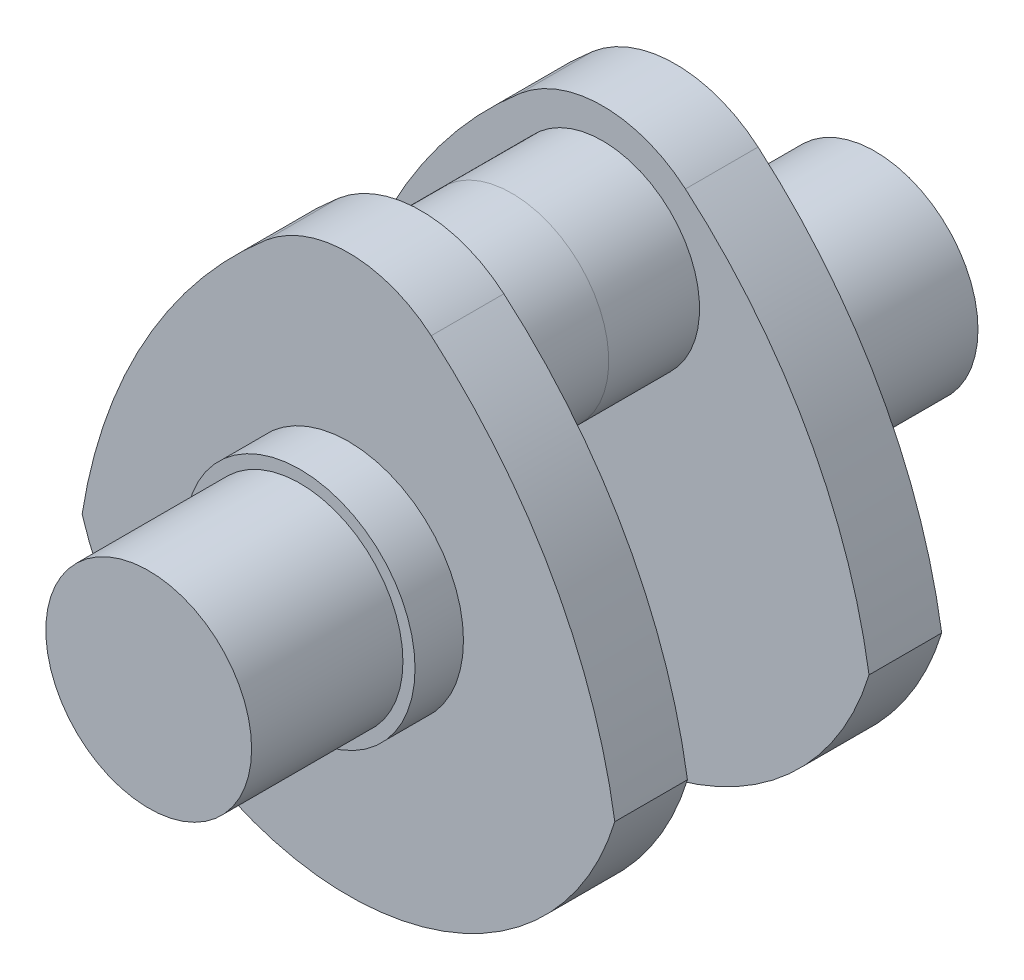
SolidWorks part; units mm, degrees
ref_plane "Front Plane" through (0, 0, 0) normal (0, 0, 1) x (1, 0, 0)
ref_plane "Top Plane" through (0, 0, 0) normal (0, 1, 0) x (1, 0, 0)
ref_plane "Right Plane" through (0, 0, 0) normal (1, 0, 0) x (0, 0, -1)
sketch "Sketch1" plane through (0, 0, 0) normal (0, 0, 1) x (1, 0, 0)
  circle A0 centre (0, 0) radius 17
  dimension "D1" = 34
extrude "Boss-Extrude1" add sketch "Sketch1" along normal blind 25
sketch "Sketch2" plane through (0, 0, 0) normal (0, 0, 1) x (1, 0, 0)
  circle A0 centre (0, 0) radius 19
  dimension "D1" = 38
extrude "Boss-Extrude2" add sketch "Sketch2" against normal blind 8
sketch "Sketch3" plane through (0, 0, -8) normal (0, 0, -1) x (-1, 0, 0)
  arc A0 (-44, -13.4164) -> (44, -13.4164) centre (0, 0) ccw
  arc A1 (13.6681, 40.9431) -> (-13.6681, 40.9431) centre (0, 25) ccw
  arc A2 (-13.6681, 40.9431) -> (-44, -13.4164) centre (44.9095, -27.3845) ccw
  arc A3 (13.6681, 40.9431) -> (44, -13.4164) centre (-44.9095, -27.3845) cw
  point P11 (-42.535, -13.4164)
  dimension "D2" = 46
  dimension "D3" = 42
  dimension "D5" = 90
  dimension "D6" = 90
  dimension "D1" = 88
  dimension "D4" = 25
extrude "Boss-Extrude3" add sketch "Sketch3" along normal blind 12
sketch "Sketch4" plane through (0, 0, -20) normal (0, 0, -1) x (-1, 0, 0)
  circle A0 centre (0, 25) radius 16
  point P2 (0, 0)
  point P5 (0, 0)
  dimension "D1" = 32
  dimension "D2" = 25
extrude "Boss-Extrude4" add sketch "Sketch4" along normal blind 15
mirror "Mirror1" about plane through (0, 25, -35) normal (0, 0, -1) of bodies 104
